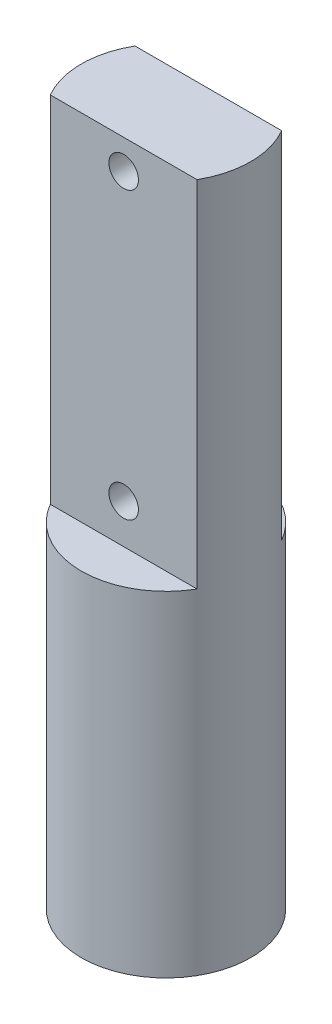
SolidWorks part; units mm, degrees
ref_plane "Front Plane" through (0, 0, 0) normal (0, 0, 1) x (1, 0, 0)
ref_plane "Top Plane" through (0, 0, 0) normal (0, 1, 0) x (1, 0, 0)
ref_plane "Right Plane" through (0, 0, 0) normal (1, 0, 0) x (0, 0, -1)
sketch "Sketch1" plane through (0, 0, 0) normal (0, 1, 0) x (1, 0, 0)
  line L0 (-4.3, 4.3) -> (4.3, 4.3)
  line L1 (-4.5, -4.5) -> (4.5, -4.5) construction
  line L2 (-4.5, -4.5) -> (-4.5, 4.5) construction
  line L3 (-4.5, 4.5) -> (4.5, 4.5) construction
  line L4 (4.5, -4.5) -> (4.5, 4.5) construction
  line L5 (4.3, -4.3) -> (4.3, 4.3)
  line L6 (-4.3, -4.3) -> (4.3, -4.3)
  line L7 (-4.3, -4.3) -> (-4.3, 4.3)
  point P0 (0, 0)
  dimension "D1" = 9
  dimension "D2" = 9
  dimension "D3" = 0.2
sketch "Sketch2" plane through (0, 0, 0) normal (0, 1, 0) x (1, 0, 0)
  circle A0 centre (0, 0) radius 4.3
extrude "Boss-Extrude2" add sketch "Sketch2" along normal blind 35
sketch "Sketch4" plane through (0, 35, 0) normal (0, 1, 0) x (1, 0, 0)
  line L0 (0, 4.3) -> (0, 0) construction
  line L1 (-4.3, 0) -> (4.3, 0) construction
  line L2 (0, 2.15) -> (-3.7239, 2.15)
  line L3 (0, 2.15) -> (3.7239, 2.15)
  line L4 (0, -2.15) -> (-3.7239, -2.15)
  line L5 (0, -2.15) -> (3.7239, -2.15)
  circle A1 centre (0, 0) radius 4.3 construction
  arc A2 (-3.7239, 2.15) -> (3.7239, 2.15) centre (0, 0) cw
  arc A3 (-3.7239, -2.15) -> (3.7239, -2.15) centre (0, 0) ccw
  point P18 (0, 0)
  point P19 (0, 0)
  point P20 (0, 0)
  point P21 (0, 0)
extrude "Cut-Extrude2" cut sketch "Sketch4" against normal blind 18
sketch "Sketch5" plane through (0, 35, 0) normal (0, 1, 0) x (1, 0, 0)
  line L2 (-3.7239, -2.15) -> (3.7239, -2.15)
  line L3 (3.7239, 2.15) -> (-3.7239, 2.15)
  line L4 (-3.7239, -2.15) -> (3.7239, -2.15)
  line L5 (3.7239, 2.15) -> (-3.7239, 2.15)
  arc A2 (3.7239, -2.15) -> (3.7239, 2.15) centre (0, 0) ccw
  arc A3 (-3.7239, 2.15) -> (-3.7239, -2.15) centre (0, 0) ccw
  arc A4 (3.7239, -2.15) -> (3.7239, 2.15) centre (0, 0) ccw
  arc A5 (-3.7239, 2.15) -> (-3.7239, -2.15) centre (0, 0) ccw
  dimension "D1" = 0
sketch "Sketch6" plane through (0, 0, 2.15) normal (0, 0, 1) x (1, 0, 0)
  line L0 (0, 17) -> (0, 17.5) construction
  line L1 (3.7239, 17) -> (-3.7239, 17) construction
  line L2 (0, 17.5) -> (-4.3, 17.5) construction
  line L3 (-4.3, 35) -> (-4.3, 0) construction
  line L4 (-4.3, 17.5) -> (-4.3, 20.5) construction
  line L5 (-4.3, 20.5) -> (4.3, 20.5) construction
  line L6 (4.3, 0) -> (4.3, 35) construction
  line L7 (4.3, 20.5) -> (4.3, 17.5) construction
  line L8 (4.3, 17.5) -> (0, 17.5) construction
  line L9 (0, 20.5) -> (0, 17.5) construction
  circle A0 centre (0, 19) radius 0.75
  dimension "D2" = 1.5
  dimension "D1" = 0.5
  dimension "D3" = 3
extrude "Cut-Extrude3" cut sketch "Sketch6" against normal blind 10
sketch "Sketch8" plane through (0, 0, 0) normal (1, 0, 0) x (0, 0, -1)
  line L0 (0, 5) -> (0, 2) construction
  line L1 (0, 2) -> (0, 0) construction
  circle A0 centre (0, 1) radius 0.75
  point P7 (0, 0)
  dimension "D2" = 1.5
  dimension "D1" = 3
extrude "Cut-Extrude5" cut sketch "Sketch8" against normal through all
sketch "Sketch9" plane through (0, 0, 2.15) normal (0, 0, 1) x (1, 0, 0)
  line L0 (0, 35) -> (0, 33.5) construction
  line L1 (-3.7239, 35) -> (3.7239, 35) construction
  circle A0 centre (0, 33.5) radius 0.75
  dimension "D1" = 1.5
extrude "Cut-Extrude6" cut sketch "Sketch9" against normal blind 10
